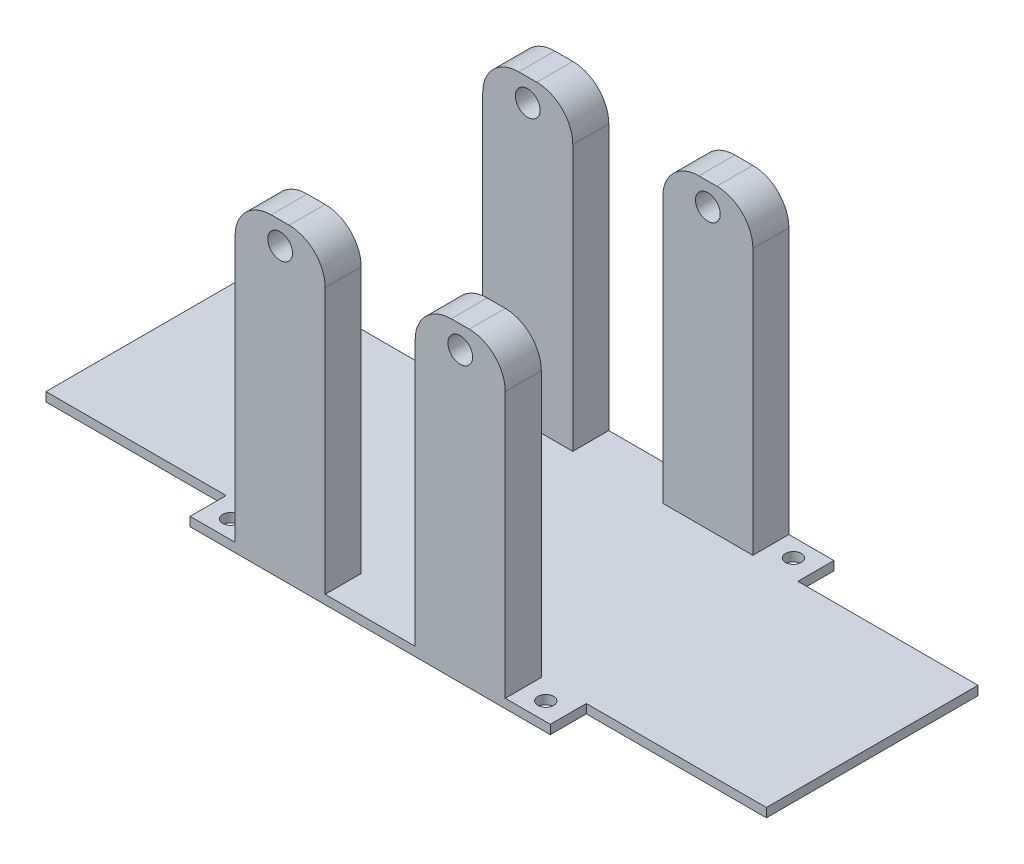
SolidWorks part; units mm, degrees
material "ABS"
ref_plane "Спереди" through (0, 0, 0) normal (0, 0, 1) x (1, 0, 0)
ref_plane "Сверху" through (0, 0, 0) normal (0, 1, 0) x (1, 0, 0)
ref_plane "Справа" through (0, 0, 0) normal (1, 0, 0) x (0, 0, -1)
sketch "Эскиз1" plane through (0, 0, 0) normal (0, 1, 0) x (1, 0, 0)
  line L0 (0, 0) -> (0, 46.182) construction
  line L1 (-80, -23.5) -> (-40, -23.5)
  line L2 (-80, -23.5) -> (-80, 23.5)
  line L3 (-80, 23.5) -> (-40, 23.5)
  line L4 (80, -23.5) -> (80, 23.5)
  line L5 (-80, -23.5) -> (80, 23.5) construction
  line L6 (-80, 23.5) -> (80, -23.5) construction
  line L7 (40, 31.5) -> (-40, 31.5)
  line L8 (40, 31.5) -> (40, 23.5)
  line L10 (-40, 31.5) -> (-40, 23.5)
  line L11 (40, 31.5) -> (-40, 23.5) construction
  line L12 (40, 23.5) -> (-40, 31.5) construction
  line L13 (40, 23.5) -> (80, 23.5)
  line L14 (0, 0) -> (84.9728, 0) construction
  line L15 (40, -31.5) -> (40, -23.5)
  line L16 (40, -31.5) -> (-40, -31.5)
  line L17 (-40, -31.5) -> (-40, -23.5)
  line L18 (40, -23.5) -> (80, -23.5)
  circle A0 centre (-35, 27.5) radius 1.75
  circle A1 centre (35, 27.5) radius 1.75
  circle A2 centre (35, -27.5) radius 1.75
  circle A3 centre (-35, -27.5) radius 1.75
  point P0 (0, 0)
  point P6 (0, 27.5)
  dimension "D5" = 5
  dimension "D7" = 3.5
  dimension "D1" = 160
  dimension "D2" = 47
  dimension "D3" = 8
  dimension "D4" = 80
  dimension "D6" = 4
  dimension "D8" = 55
extrude "Бобышка-Вытянуть1" add sketch "Эскиз1" along normal blind 2
sketch "Эскиз2" plane through (0, 2, 0) normal (0, 1, 0) x (1, 0, 0)
  line L0 (-80, 0) -> (80, 0) construction
  line L1 (-80, 23.5) -> (-80, -23.5) construction
  line L2 (80, -23.5) -> (80, 23.5) construction
  line L3 (0, -31.5) -> (0, 31.5) construction
  line L4 (-40, -31.5) -> (40, -31.5) construction
  line L5 (40, 31.5) -> (-40, 31.5) construction
  line L6 (30, -23.5) -> (10, -23.5)
  line L7 (-30, -31.5) -> (-10, -31.5)
  line L8 (-30, -31.5) -> (-30, -23.5)
  line L9 (-30, -23.5) -> (-10, -23.5)
  line L10 (-10, -31.5) -> (-10, -23.5)
  line L11 (10, -31.5) -> (10, -23.5)
  line L12 (30, -31.5) -> (10, -31.5)
  line L13 (30, -31.5) -> (30, -23.5)
  line L14 (30, 31.5) -> (30, 23.5)
  line L15 (30, 31.5) -> (10, 31.5)
  line L16 (10, 31.5) -> (10, 23.5)
  line L17 (30, 23.5) -> (10, 23.5)
  line L18 (-30, 23.5) -> (-10, 23.5)
  line L19 (-10, 31.5) -> (-10, 23.5)
  line L20 (-30, 31.5) -> (-10, 31.5)
  line L21 (-30, 31.5) -> (-30, 23.5)
  dimension "D1" = 20
  dimension "D2" = 8
  dimension "D3" = 10
extrude "Бобышка-Вытянуть2" add sketch "Эскиз2" along normal blind 67
sketch "Эскиз3" plane through (0, 0, 31.5) normal (0, 0, 1) x (1, 0, 0)
  line L0 (-30, 69) -> (-30, 2) construction
  line L1 (-30, 69) -> (-10, 69) construction
  line L2 (0, 0) -> (0, 72.9909) construction
  circle A0 centre (-20, 64) radius 2.75
  circle A1 centre (20, 64) radius 2.75
  dimension "D1" = 5.5
  dimension "D2" = 10
  dimension "D3" = 5
extrude "Вырез-Вытянуть1" cut sketch "Эскиз3" against normal through all and the other way through all
fillet "Скругление1" radius 8 8 edges at (30, 69, -27.5) (10, 69, -27.5) (-30, 69, -27.5) (-30, 69, 27.5) (10, 69, 27.5) (30, 69, 27.5) (-10, 69, -27.5) (-10, 69, 27.5)
